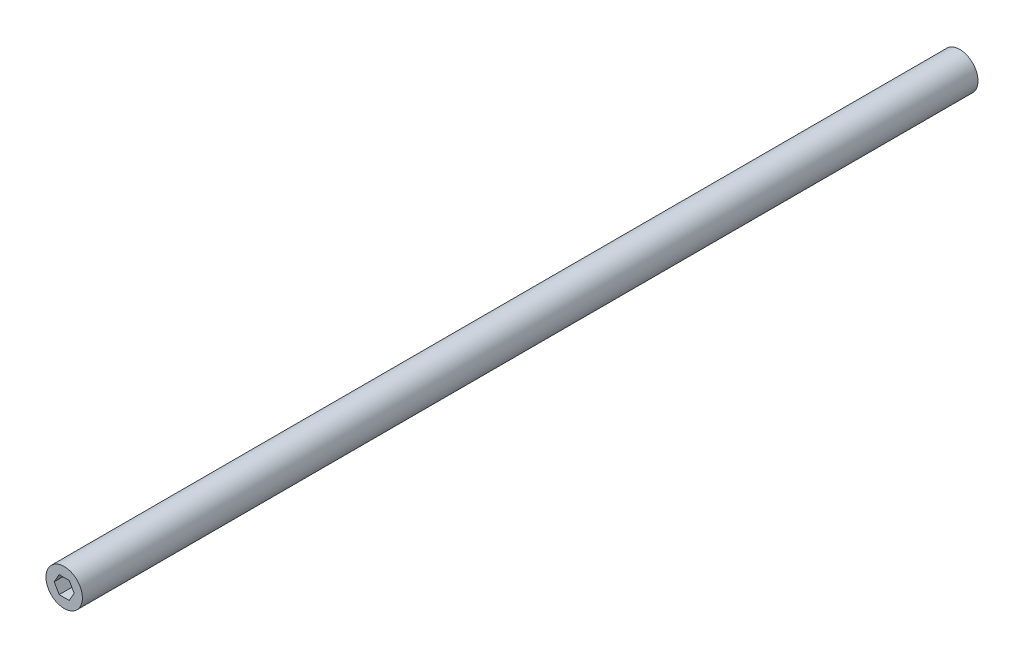
SolidWorks part; units mm, degrees
ref_plane "Front Plane" through (0, 0, 0) normal (0, 0, 1) x (1, 0, 0)
ref_plane "Top Plane" through (0, 0, 0) normal (0, 1, 0) x (1, 0, 0)
ref_plane "Right Plane" through (0, 0, 0) normal (1, 0, 0) x (0, 0, -1)
sketch "Sketch2" plane through (0, 0, 0) normal (0, 0, 1) x (1, 0, 0)
  line L1 (-43.1031, 15.7984) -> (-50.0578, 15.7901)
  line L2 (-50.0578, 15.7901) -> (-53.528, 9.7629)
  line L3 (-53.528, 9.7629) -> (-50.0434, 3.7441)
  line L4 (-50.0434, 3.7441) -> (-43.0887, 3.7524)
  line L5 (-43.0887, 3.7524) -> (-39.6185, 9.7796)
  line L6 (-39.6185, 9.7796) -> (-43.1031, 15.7984)
  circle A0 centre (-46.5732, 9.7712) radius 12.659
  circle A1 centre (-46.5732, 9.7712) radius 6.023 construction
extrude "Boss-Extrude4" add sketch "Sketch2" along normal blind 622.3
